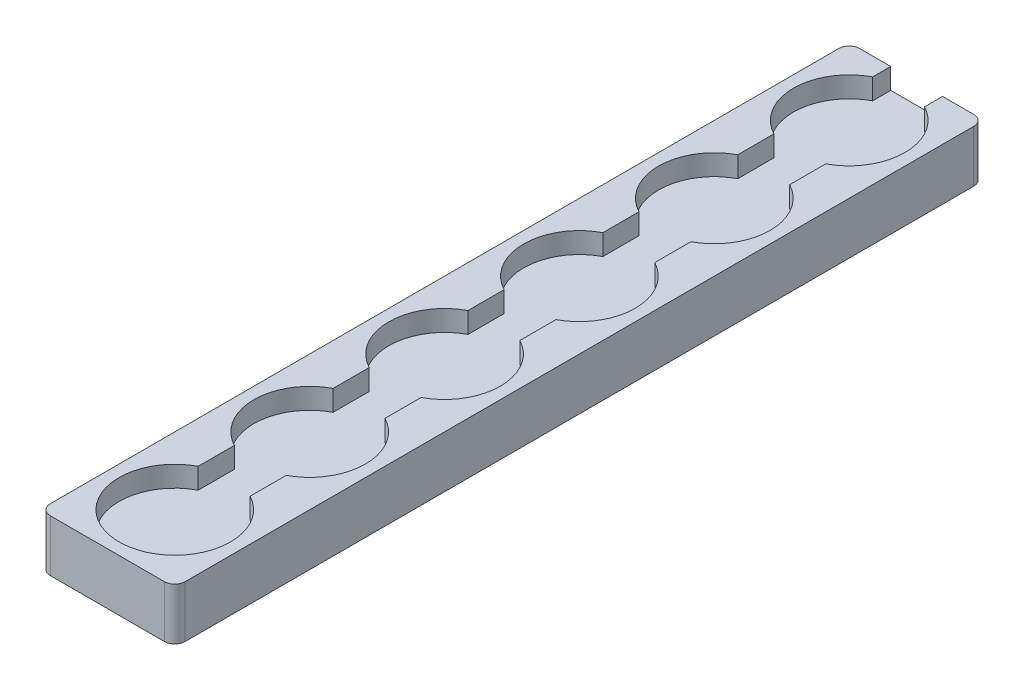
SolidWorks part; units mm, degrees
material "ABS"
ref_plane "Front Plane" through (0, 0, 0) normal (0, 0, 1) x (1, 0, 0)
ref_plane "Top Plane" through (0, 0, 0) normal (0, 1, 0) x (1, 0, 0)
ref_plane "Right Plane" through (0, 0, 0) normal (1, 0, 0) x (0, 0, -1)
sketch "Sketch4" plane through (0, 0, 0) normal (0, 1, 0) x (1, 0, 0)
  circle A0 centre (0, 0) radius 10.75
  dimension "D1" = 21.5
sketch "Sketch5" plane through (0, 0, 0) normal (0, 1, 0) x (1, 0, 0)
  line L1 (-13, 13) -> (13, 13)
  line L2 (-13, 13) -> (-13, -13)
  line L3 (-13, -13) -> (13, -13)
  line L4 (13, 13) -> (13, -13)
  dimension "D1" = 13
  dimension "D2" = 13
  dimension "D3" = 26
  dimension "D4" = 26
extrude "Boss-Extrude1" add sketch "Sketch5" against normal blind 10
extrude "Cut-Extrude1" cut sketch "Sketch4" against normal blind 4 contours A0
sketch "Sketch6" plane through (0, 0, 0) normal (0, 1, 0) x (1, 0, 0)
  line L0 (13, 13) -> (-13, 13) construction
  line L1 (-5, 13) -> (5, 13)
  line L2 (-5, 13) -> (-5, 9.5164)
  line L3 (-5, 9.5164) -> (5, 9.5164)
  line L4 (5, 13) -> (5, 9.5164)
  line L5 (-13, 13) -> (-13, -13) construction
  circle A0 centre (0, 0) radius 10.75 construction
  dimension "D1" = 10
  dimension "D2" = 8
extrude "Cut-Extrude2" cut sketch "Sketch6" against normal blind 4 contours L2 L3 L4 L1
pattern_linear "LPattern1" count 6 spacing 26 along (0, 0, -1) of "Boss-Extrude1", "Cut-Extrude1", "Cut-Extrude2"
sketch "Sketch7" plane through (0, 0, -13) normal (0, 0, 1) x (1, 0, 0)
  line L0 (-5, -4) -> (5, -4) construction
  line L1 (-5, 0) -> (5, 0)
  line L2 (-5, 0) -> (-5, -4)
  line L3 (-5, -4) -> (5, -4)
  line L4 (5, 0) -> (5, -4)
extrude "Cut-Extrude3" cut sketch "Sketch7" against normal through all
fillet "Fillet1" radius 2 4 edges at (13, -5, -143) (-13, -5, -143) (13, -5, 13) (-13, -5, 13)
sketch "Sketch9" plane through (0, 0, -143) normal (0, 0, -1) x (-1, 0, 0)
  line L0 (5, -4) -> (-5, -4) construction
  line L1 (-4, -5.5) -> (4, -5.5)
  line L2 (-4, -5.5) -> (-4, -8.5)
  line L3 (-4, -8.5) -> (4, -8.5)
  line L4 (4, -5.5) -> (4, -8.5)
  line L5 (-5, -4) -> (-5, 0) construction
  point P4 (4, -7)
  dimension "D1" = 3
  dimension "D2" = 8
  dimension "D3" = 3
  dimension "D4" = 1
extrude "Cut-Extrude4" cut sketch "Sketch9" against normal blind 3
